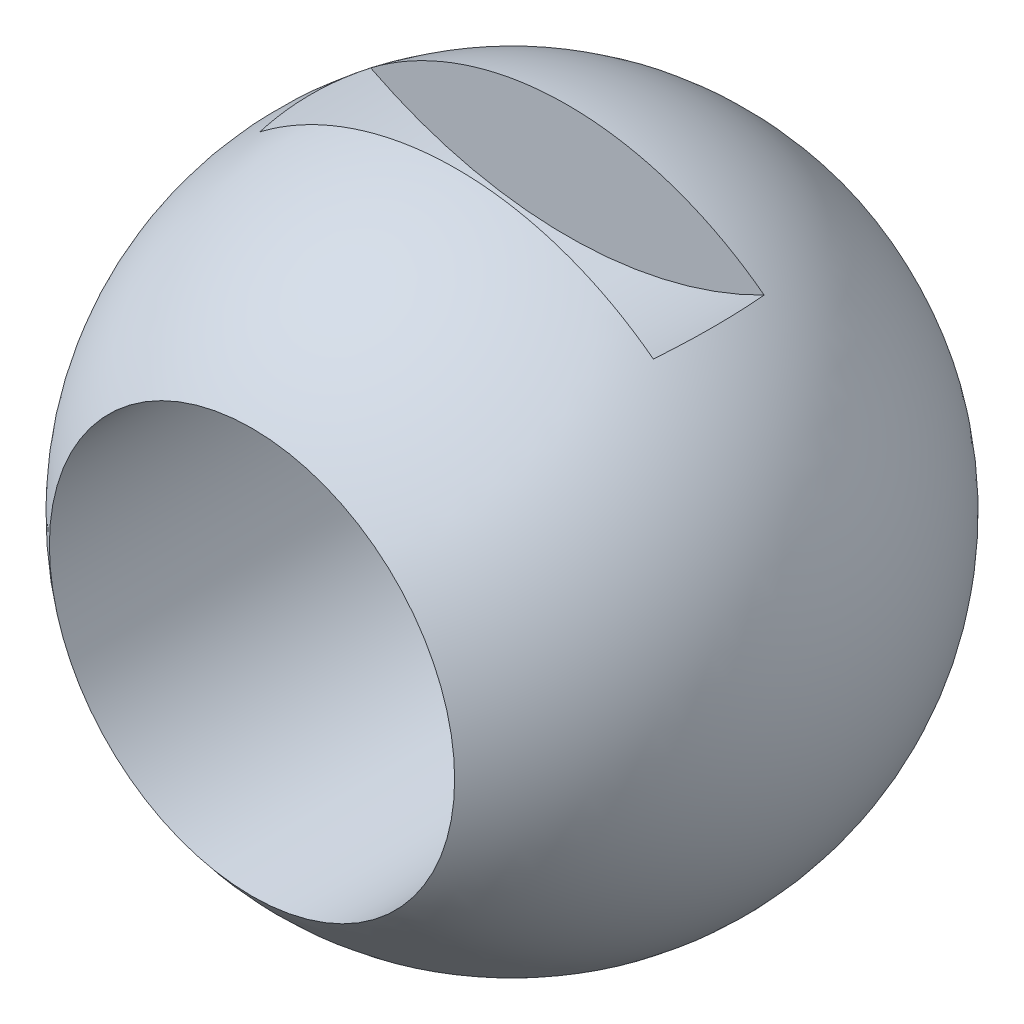
SolidWorks part; units mm, degrees
material "AISI 304"
ref_plane "Front Plane" through (0, 0, 0) normal (0, 0, 1) x (1, 0, 0)
ref_plane "Top Plane" through (0, 0, 0) normal (0, 1, 0) x (1, 0, 0)
ref_plane "Right Plane" through (0, 0, 0) normal (1, 0, 0) x (0, 0, -1)
sketch "Sketch1" plane through (0, 0, 0) normal (0, 0, 1) x (1, 0, 0)
  line L0 (0, 15.494) -> (0, -15.494)
  arc A0 (0, 15.494) -> (0, -15.494) centre (0, 0) ccw
  dimension "D1" = 30.988
revolve "Revolve1" add sketch "Sketch1" angle 360 about L0
sketch "Sketch2" plane through (0, 0, 0) normal (0, 0, 1) x (1, 0, 0)
  line L0 (0, -10.7346) -> (0, 21.4691) construction
  line L5 (0, 10.7235) -> (0, 21.7885) construction
  line L6 (-3.7768, 15.494) -> (3.7768, 15.494) construction
  line L7 (-14.3358, 15.494) -> (14.6743, 15.494)
  line L9 (-11.43, 15.494) -> (11.43, 15.494)
  line L10 (-11.43, 15.494) -> (-11.43, 12.2682)
  line L11 (-11.43, 12.2682) -> (11.43, 12.2682)
  line L12 (11.43, 15.494) -> (11.43, 12.2682)
  circle A0 centre (0, 0) radius 15.494 construction
  point P0 (0, 15.494)
  point P11 (0, 12.2682)
  dimension "D1" = 3.2258
  dimension "D2" = 22.86
extrude "Cut-Extrude1" cut sketch "Sketch2" against normal mid plane 5.207 contours L12 L7 L10 L11
sketch "Sketch3" plane through (0, 0, 0) normal (0, 0, 1) x (1, 0, 0)
  line L2 (-9.4634, 12.2682) -> (9.4634, 12.2682)
  arc A0 (-9.4634, 12.2682) -> (9.4634, 12.2682) centre (0, 30.2501) ccw
  arc A1 (-9.4634, 12.2682) -> (9.4634, 12.2682) centre (0, 0) ccw construction
  dimension "D1" = 20.32
extrude "Cut-Extrude2" cut sketch "Sketch3" against normal mid plane 5.207
sketch "Sketch4" plane through (0, 0, 0) normal (0, 0, 1) x (1, 0, 0)
  circle A0 centre (0, 0) radius 9.525
  dimension "D1" = 19.05
extrude "Cut-Extrude3" cut sketch "Sketch4" against normal through all both and the other way through all
